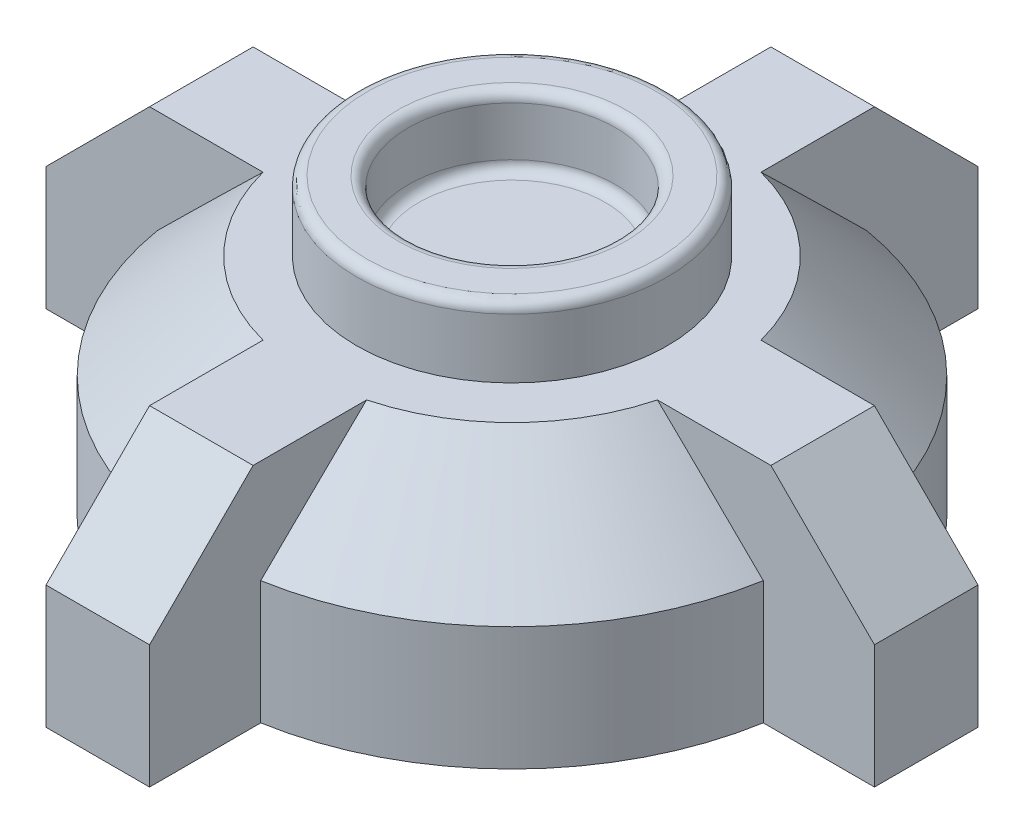
SolidWorks part; units mm, degrees
ref_plane "Alzado" through (0, 0, 0) normal (0, 0, 1) x (1, 0, 0)
ref_plane "Planta" through (0, 0, 0) normal (0, 1, 0) x (1, 0, 0)
ref_plane "Vista lateral" through (0, 0, 0) normal (1, 0, 0) x (0, 0, -1)
sketch "Croquis1" plane through (0, 0, 0) normal (0, 1, 0) x (1, 0, 0)
  line L0 (-10, -58.5304) -> (-10, -80)
  line L1 (-10, 80) -> (10, 80)
  line L2 (-10, 80) -> (-10, 58.5304)
  line L3 (-10, -80) -> (10, -80)
  line L4 (10, 80) -> (10, 58.5304)
  line L5 (58.5304, 10) -> (80, 10)
  line L6 (-80, -10) -> (-58.5304, -10)
  line L7 (-80, -10) -> (-80, 10)
  line L8 (-80, 10) -> (-58.5304, 10)
  line L9 (10, -58.5304) -> (10, -80)
  line L10 (80, -10) -> (80, 10)
  line L15 (58.5304, -10) -> (80, -10)
  arc A0 (-10, 58.5304) -> (-58.5304, 10) centre (0, 0) ccw
  circle A1 centre (0, 42) radius 1.8585
  arc A2 (10, -58.5304) -> (58.5304, -10) centre (0, 0) ccw
  arc A3 (-58.5304, -10) -> (-10, -58.5304) centre (0, 0) ccw
  arc A4 (58.5304, 10) -> (10, 58.5304) centre (0, 0) ccw
  dimension "D1" = 42
  dimension "D6" = 80
  dimension "D2" = 160
  dimension "D3" = 20
  dimension "D4" = 20
  dimension "D5" = 160
  dimension "D7" = 80
  dimension "D8" = 10
  dimension "D9" = 10
extrude "Saliente-Extruir1" add sketch "Croquis1" along normal blind 43.8 contours A0 L8 L7 L6 A3 L0 L3 L9 A2 L15 L10 L5 A4 L4 L1 L2
chamfer "Chaflán1" distance 20 8 edges at (0, 43.8, -80) (-41.987, 43.8, -41.987) (-80, 43.8, 0) (-41.987, 43.8, 41.987) (41.987, 43.8, 41.987) (41.987, 43.8, -41.987) (80, 43.8, 0) (0, 43.8, 80)
sketch "Croquis2" plane through (0, 43.8, 0) normal (0, 1, 0) x (1, 0, 0)
  circle A0 centre (0, 0) radius 30
  circle A1 centre (0, 0) radius 20
extrude "Saliente-Extruir2" add sketch "Croquis2" along normal blind 13.5
fillet "Redondeo1" radius 2 3 edges at (0, 57.3, 30) (0, 57.3, 20) (0, 43.8, 20)
